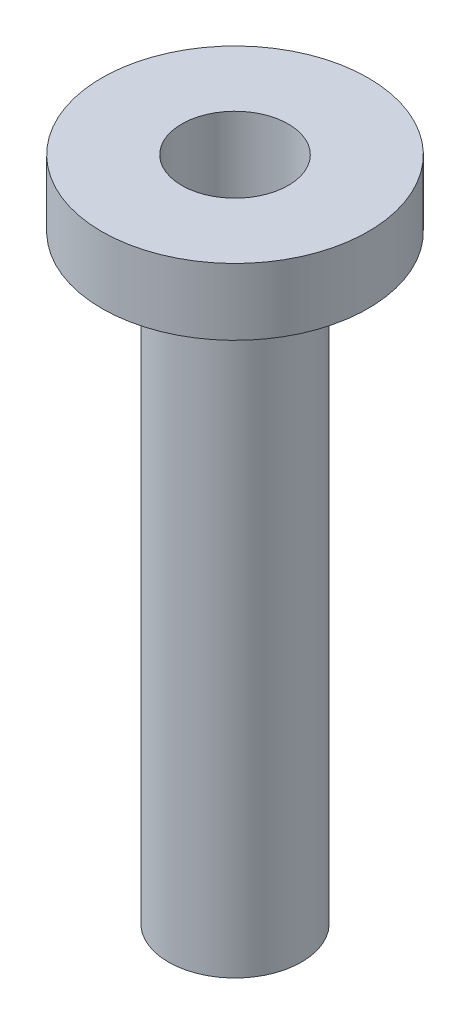
SolidWorks part; units mm, degrees
ref_plane "Front Plane" through (0, 0, 0) normal (0, 0, 1) x (1, 0, 0)
ref_plane "Top Plane" through (0, 0, 0) normal (0, 1, 0) x (1, 0, 0)
ref_plane "Right Plane" through (0, 0, 0) normal (1, 0, 0) x (0, 0, -1)
sketch "Sketch1" plane through (0, 0, 0) normal (0, 0, 1) x (1, 0, 0)
  line L0 (-5.08, 0) -> (-12.7, 0)
  line L1 (-12.7, 0) -> (-12.7, -6.35)
  line L2 (-12.7, -6.35) -> (-11.1125, -6.35)
  line L3 (-11.1125, -6.35) -> (-11.1125, -4.318)
  line L4 (-11.1125, -4.318) -> (-8.0645, -4.318)
  line L5 (-8.0645, -4.318) -> (-8.0645, -6.35)
  line L6 (-8.0645, -6.35) -> (-6.35, -6.35)
  line L7 (-6.35, -6.35) -> (-6.35, -63.5)
  line L8 (-6.35, -63.5) -> (-5.08, -62.23)
  line L9 (-5.08, -62.23) -> (-5.08, 0)
  line L10 (0, 0) -> (0, -4.7723) construction
  dimension "D1" = 1.5875
  dimension "D2" = 2.032
  dimension "D3" = 3.048
  dimension "D4" = 12.7
  dimension "D5" = 5.08
  dimension "D6" = 6.35
  dimension "D7" = 45
  dimension "D8" = 57.15
  dimension "D9" = 6.35
revolve "Revolve1" add sketch "Sketch1" angle 360 about L10
